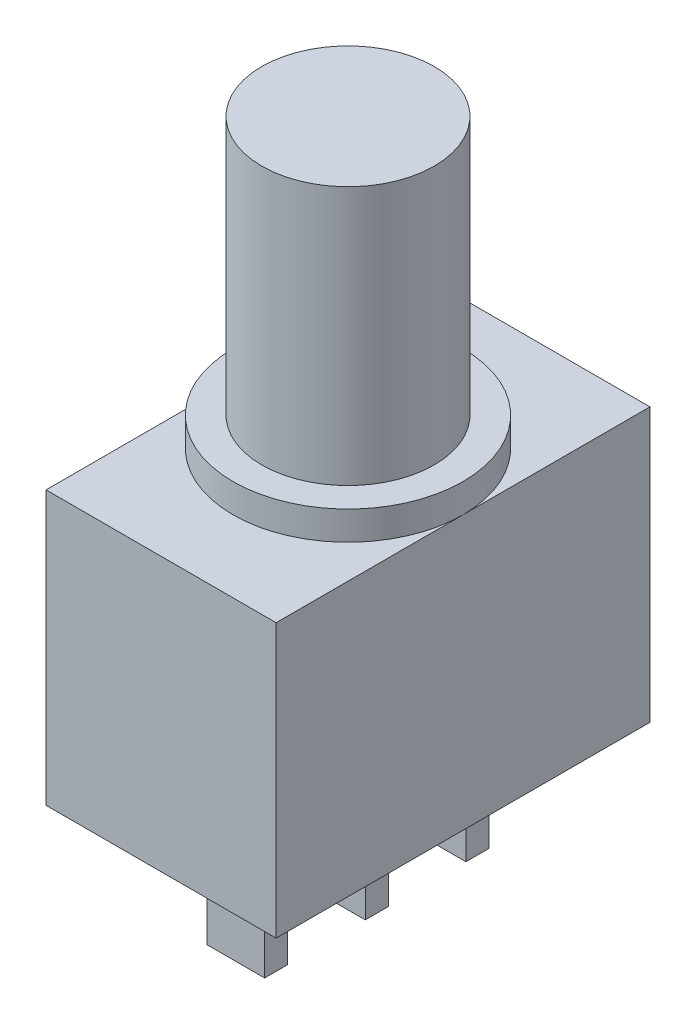
SolidWorks part; units mm, degrees
ref_plane "Plan de face" through (0, 0, 0) normal (0, 0, 1) x (1, 0, 0)
ref_plane "Plan de dessus" through (0, 0, 0) normal (0, 1, 0) x (1, 0, 0)
ref_plane "Plan de droite" through (0, 0, 0) normal (1, 0, 0) x (0, 0, -1)
sketch "Esquisse1" plane through (0, 0, 0) normal (1, 0, 0) x (0, 0, -1)
  line L1 (0, 0) -> (13, 0)
  line L2 (0, 0) -> (0, 9.5)
  line L3 (0, 9.5) -> (13, 9.5)
  line L4 (13, 0) -> (13, 9.5)
  dimension "D1" = 9.5
  dimension "D2" = 13
extrude "Boss.-Extru.1" add sketch "Esquisse1" along normal blind 8
sketch "Esquisse2" plane through (0, 9.5, 0) normal (0, 1, 0) x (1, 0, 0)
  line L0 (8, 13) -> (8, 0) construction
  line L1 (8, 0) -> (0, 0) construction
  circle A0 centre (4, 6.5) radius 4
  dimension "D1" = 8
  dimension "D2" = 4
  dimension "D3" = 6.5
extrude "Boss.-Extru.2" add sketch "Esquisse2" along normal blind 1
sketch "Esquisse3" plane through (0, 10.5, 0) normal (0, 1, 0) x (1, 0, 0)
  circle A0 centre (4, 6.5) radius 3
  dimension "D1" = 6
extrude "Boss.-Extru.3" add sketch "Esquisse3" along normal blind 9
sketch "Esquisse4" plane through (0, 0, 0) normal (0, -1, 0) x (1, 0, 0)
  line L0 (0, 0) -> (0, -13) construction
  line L1 (5, -2.6) -> (3, -2.6)
  line L2 (5, -2.6) -> (5, -3.4)
  line L3 (5, -3.4) -> (3, -3.4)
  line L4 (3, -2.6) -> (3, -3.4)
  line L5 (5, -6.1) -> (3, -6.1)
  line L6 (5, -6.1) -> (5, -6.9)
  line L7 (5, -6.9) -> (3, -6.9)
  line L8 (3, -6.1) -> (3, -6.9)
  line L9 (5, -9.6) -> (3, -9.6)
  line L10 (5, -9.6) -> (5, -10.4)
  line L11 (5, -10.4) -> (3, -10.4)
  line L12 (3, -9.6) -> (3, -10.4)
  line L14 (8, 0) -> (0, 0) construction
  line L15 (8, -13) -> (0, -13) construction
  dimension "D1" = 0.8
  dimension "D2" = 0.8
  dimension "D3" = 0.8
  dimension "D4" = 2
  dimension "D5" = 2
  dimension "D6" = 2
  dimension "D7" = 3
  dimension "D8" = 3
  dimension "D9" = 3
  dimension "D10" = 2.6
  dimension "D11" = 2.6
  dimension "D12" = 2.7
  dimension "D13" = 2.7
extrude "Boss.-Extru.4" add sketch "Esquisse4" along normal blind 4
